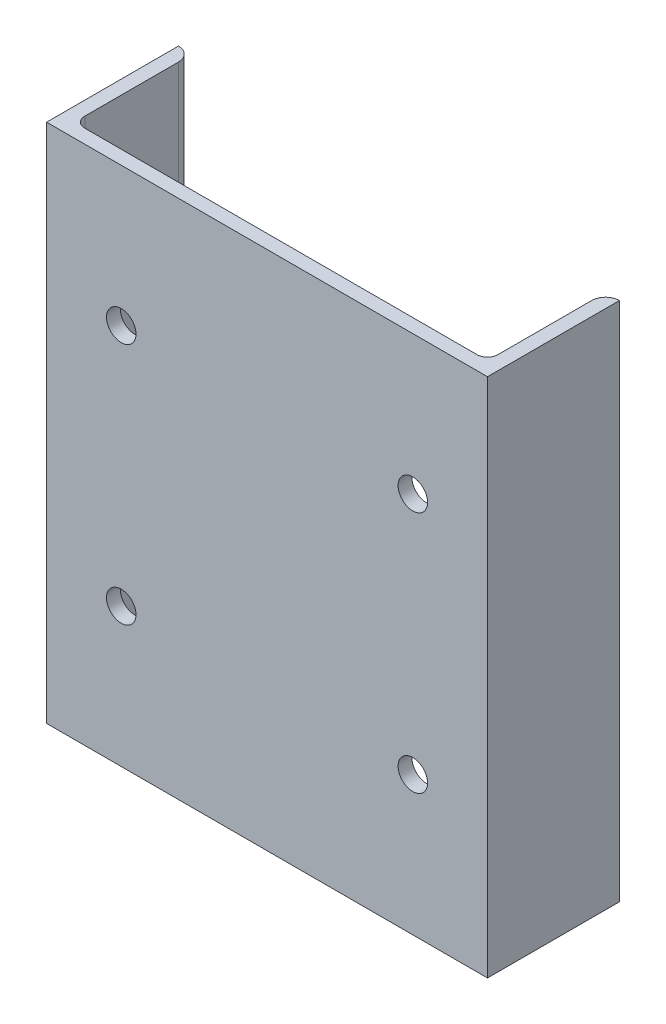
SolidWorks part; units mm, degrees
ref_plane "Front Plane" through (0, 0, 0) normal (0, 0, 1) x (1, 0, 0)
ref_plane "Top Plane" through (0, 0, 0) normal (0, 1, 0) x (1, 0, 0)
ref_plane "Right Plane" through (0, 0, 0) normal (1, 0, 0) x (0, 0, -1)
sketch "Sketch1" plane through (0, 0, 0) normal (0, 1, 0) x (1, 0, 0)
  line L0 (-127, 0) -> (127, 0)
  line L1 (-127, 0) -> (-127, 76)
  line L2 (127, 0) -> (127, 76)
  line L3 (-113, 8) -> (113, 8)
  line L4 (119, 14) -> (119, 68)
  line L5 (-119, 14) -> (-119, 68)
  arc A0 (113, 8) -> (119, 14) centre (113, 14) ccw
  arc A1 (-113, 8) -> (-119, 14) centre (-113, 14) cw
  arc A2 (119, 68) -> (127, 76) centre (127, 68) cw
  arc A3 (-119, 68) -> (-127, 76) centre (-127, 68) ccw
  point P11 (119, 8)
  point P14 (-119, 8)
  dimension "D6" = 6
  dimension "D7" = 6
  dimension "D1" = 254
  dimension "D2" = 238
  dimension "D3" = 60
  dimension "D4" = 76
  dimension "D5" = 8
  dimension "D8" = 127
  dimension "D9" = 119
extrude "Extrude1" add sketch "Sketch1" along normal mid plane 300
sketch "Sketch2" plane through (0, 0, 0) normal (0, 0, 1) x (1, 0, 0)
  line L0 (127, 150) -> (127, -150) construction
  circle A0 centre (84, 70) radius 8.5
  circle A1 centre (-84, 70) radius 8.5
  circle A2 centre (-84, -70) radius 8.5
  circle A3 centre (84, -70) radius 8.5
  dimension "D1" = 17
  dimension "D2" = 70
  dimension "D3" = 70
  dimension "D4" = 70
  dimension "D5" = 70
  dimension "D6" = 43
  dimension "D7" = 43
  dimension "D8" = 168
  dimension "D9" = 168
extrude "Cut-Extrude1" cut sketch "Sketch2" against normal up to next
